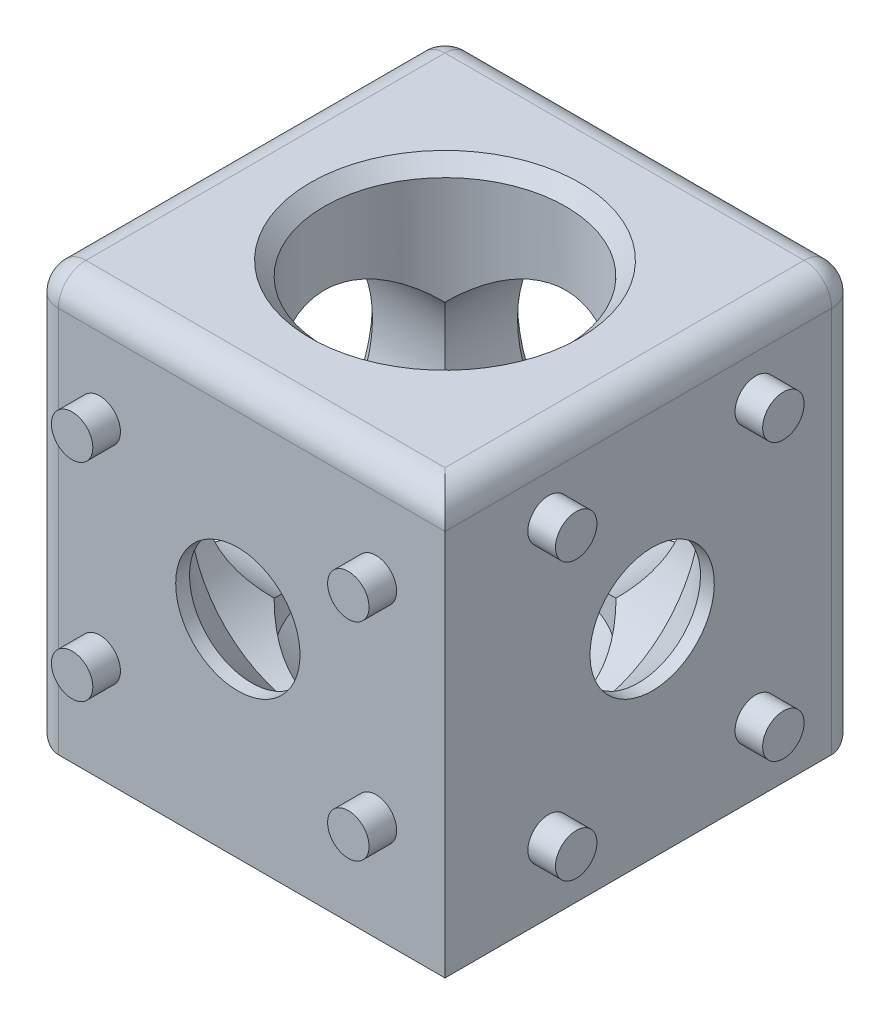
SolidWorks part; units mm, degrees
material "Алюминиевый сплав"
ref_plane "Спереди" through (0, 0, 0) normal (0, 0, 1) x (1, 0, 0)
ref_plane "Сверху" through (0, 0, 0) normal (0, 1, 0) x (1, 0, 0)
ref_plane "Справа" through (0, 0, 0) normal (1, 0, 0) x (0, 0, -1)
sketch "Эскиз1" plane through (0, 0, 0) normal (0, 1, 0) x (1, 0, 0)
  line L1 (-15, -15) -> (15, -15)
  line L2 (-15, -15) -> (-15, 15)
  line L3 (-15, 15) -> (15, 15)
  line L4 (15, -15) -> (15, 15)
  line L5 (-15, -15) -> (15, 15) construction
  line L6 (-15, 15) -> (15, -15) construction
  point P0 (0, 0)
  dimension "D1" = 30
extrude "Бобышка-Вытянуть1" add sketch "Эскиз1" along normal mid plane 30
sketch "Эскиз4" plane through (0, 0, 0) normal (0, 0, 1) x (1, 0, 0)
  line L0 (-4.5, -15) -> (-4.5, -14)
  line L1 (-15, -15) -> (15, -15) construction
  line L2 (-4.5, -14) -> (-8.75, -9.75)
  line L3 (-8.75, -9.75) -> (-8.75, 14)
  line L4 (-15, 15) -> (15, 15) construction
  line L6 (0, 15) -> (0, -15) construction
  line L7 (0, -15) -> (-4.5, -15)
  line L8 (0, 15) -> (0, -15)
  line L9 (-8.75, 14) -> (-9.75, 15)
  line L10 (-9.75, 15) -> (0, 15)
  dimension "D1" = 9
  dimension "D2" = 45
  dimension "D3" = 17.5
  dimension "D4" = 1
  dimension "D5" = 1
revolve "Вырез-Повернуть1" cut sketch "Эскиз4" angle 360 about L6
sketch "Эскиз5" plane through (0, -15, 0) normal (0, -1, 0) x (1, 0, 0)
  line L1 (-10, 7.5) -> (10, 7.5) construction
  line L2 (-10, 7.5) -> (-10, -7.5) construction
  line L3 (-10, -7.5) -> (10, -7.5) construction
  line L4 (10, 7.5) -> (10, -7.5) construction
  circle A0 centre (-10, 7.5) radius 1.5
  circle A1 centre (-10, -7.5) radius 1.5
  circle A2 centre (10, -7.5) radius 1.5
  circle A3 centre (10, 7.5) radius 1.5
  point P5 (-10, 0)
  point P12 (0, 7.5)
  dimension "D1" = 3
  dimension "D2" = 20
  dimension "D3" = 15
extrude "Бобышка-Вытянуть2" add sketch "Эскиз5" along normal blind 2
ref_plane "Плоскость1" through (0, 0, 0) normal (0.7071, 0.7071, 0) x (0.7071, -0.7071, 0)
ref_plane "Плоскость2" through (0, 0, 0) normal (0, 0.7071, 0.7071) x (1, 0, 0)
mirror "Зеркальное отражение1" about plane through (0, 0, 0) normal (0.7071, 0.7071, 0) of "Бобышка-Вытянуть2", "Вырез-Повернуть1"
fillet "Скругление1" radius 2 9 edges at (-15, -15, 0) (15, 15, 0) (-15, 0, 15) (0, 15, 15) (-15, 15, 0) (-15, 0, -15) (0, 15, -15) (0, -15, -15) (15, 0, -15)
mirror "Зеркальное отражение2" about plane through (0, 0, 0) normal (0, 0.7071, 0.7071) of "Бобышка-Вытянуть2", "Вырез-Повернуть1"
